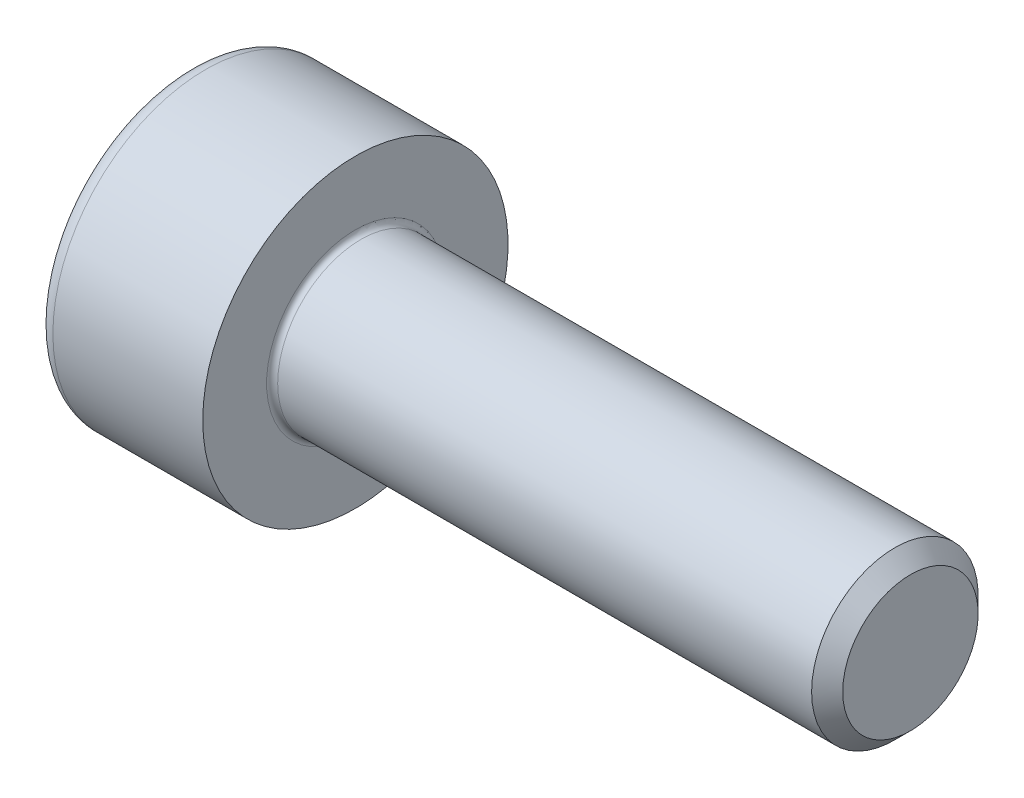
SolidWorks part; units mm, degrees
revolve "Base-Revolve" add sketch "BodySke"
sketch "BodySke" plane through (0, 0, 0) normal (0, 0, 1) x (1, 0, 0)
  line L0 (0, 0) -> (0, 2.75)
  line L1 (0, 2.75) -> (3, 2.75)
  line L2 (3, 2.75) -> (3, 1.5)
  line L3 (3, 1.5) -> (12.7195, 1.5)
  line L4 (13, 1.2195) -> (13, 0)
  line L5 (13, 0) -> (0, 0)
  line L6 (-31.75, 0) -> (127, 0) construction
  line L8 (13, 1.2195) -> (12.7195, 1.5)
  line L10 (13, -1.2195) -> (12.7195, -1.5) construction
  line L11 (3.5, 9.525) -> (3.5, 3.175) construction
  line L12 (3, 9.525) -> (3, 3.175) construction
  line L13 (-47, 9.525) -> (-47, 3.175) construction
  dimension "Head_ht" = 3
  dimension "Length" = 10
  dimension "Body_ch_ang" = 45
  dimension "Diameter" = 3
  dimension "Minor_dia" = 2.439
  dimension "Advance" = 0.5
  dimension "Thread_nom" = 10
  dimension "Thread_length" = 60
  dimension "Head_dia" = 5.5
cosmetic thread "ThreadCosmetic" [suppressed]
fillet "Fillet1" radius 0.1 1 edges at (3, 0, 1.5)
fillet "Fillet2" radius 0.3 1 edges at (0, 0, 2.75)
ref_plane "Plane1" through (0, 0, 0) normal (0, 0, 1) x (1, 0, 0)
ref_plane "Plane2" through (0, 0, 0) normal (0, 1, 0) x (1, 0, 0)
ref_plane "Plane3" through (0, 0, 0) normal (1, 0, 0) x (0, 0, -1)
sketch "Sketch2" plane through (0, 0, 0) normal (0, 0, 1) x (1, 0, 0)
  line L0 (0, 1.26) -> (1.3, 1.26)
  line L1 (1.3, 1.26) -> (2.0275, 0)
  line L2 (-31.75, 0) -> (127, 0) construction
  line L3 (2.0275, 0) -> (0, 0)
  line L4 (0, 0) -> (0, 1.26)
  line L6 (0, 0) -> (47.625, 0) construction
  dimension "D1" = 1.26
  dimension "D2" = 60
  dimension "Depth" = 1.3
revolve "Hex-PreBroach" cut sketch "Sketch2" angle 360 about L6
sketch "Sketch3" plane through (0, 0, 0) normal (-1, 0, 0) x (0, 0.5, 0.866)
  line L0 (0.7275, 1.26) -> (-0.7275, 1.26)
  line L1 (-0.7275, 1.26) -> (-1.4549, 0)
  line L2 (0.7275, 1.26) -> (1.4549, 0)
  line L3 (0.7275, -1.26) -> (1.4549, 0)
  line L4 (0.7275, -1.26) -> (-0.7275, -1.26)
  line L5 (-0.7275, -1.26) -> (-1.4549, 0)
  dimension "D1" = 1.26
  dimension "D2" = 1.26
  dimension "Hex_size" = 2.52
extrude "Hex" cut sketch "Sketch3" against normal blind 1.3
sketch "ThdSchSke" plane through (0, 0, 0) normal (0, 0, 1) x (1, 0, 0)
  line L0 (4.5, -1.2195) -> (4.3036, -1.5)
  line L1 (4.5, -1.2195) -> (4.6964, -1.5)
  line L2 (4.6964, -1.5) -> (4.6964, -1.875)
  line L3 (-3.175, 0) -> (5.1513, 0) construction
  line L4 (0, 2.45) -> (0, -2.45) construction
  line L5 (4.6964, -1.875) -> (4.3036, -1.875)
  line L6 (4.3036, -1.875) -> (4.3036, -1.5)
  dimension "Thread_minor" = 2.439
  dimension "Diameter" = 3
  dimension "Start" = 4.5
revolve "ThreadSchematic" [suppressed] cut sketch "ThdSchSke" angle 360 about L3
pattern_linear "ThdSchPat" [suppressed]
equation "\"D2@Sketch3\" = \"Hex_size@Sketch3\" / 2"
equation "\"D1@Sketch3\" = \"Hex_size@Sketch3\" / 2"
equation "\"D1@Sketch2\" = \"Hex_size@Sketch3\" / 2"
equation "\"Thread_minor@ThreadCosmetic\"  =  \"Minor_dia@BodySke\""
equation "\"Depth@Sketch2\" =  \"Key_eng@Hex\""
equation "\"Thread_length@ThreadCosmetic\" = ((sgn( (\"Length@BodySke\" - \"Advance@BodySke\" * 3.0) - \"Thread_nom@BodySke\" )-1)*( (\"Length@BodySke\" - \"Advance@BodySke\" * 3.0) - \"Thread_nom@BodySke\" ))/-2+ \"Thread_nom@BodySke\""
equation "\"Thread_minor@ThdSchSke\" = \"Minor_dia@BodySke\""
equation "\"Diameter@ThdSchSke\" = \"Diameter@BodySke\""
equation "\"Overcut@ThdSchSke\" = \"Diameter@BodySke\" * 1.25"
equation "\"Start@ThdSchSke\" = \"Head_ht@BodySke\" + \"Length@BodySke\" - \"Thread_length@ThreadCosmetic\"  '---Non-countersunk---"
equation "\"Num_threads@ThdSchPat\" = int( \"Thread_length@ThreadCosmetic\" / \"Advance@BodySke\" + 0.999 )  + 1"
equation "\"Advance@ThdSchPat\" = \"Thread_length@ThreadCosmetic\" /  (\"Num_threads@ThdSchPat\" - 1) 'relax it"
equation "\"Num_threads@ThdSchPat\" = \"Num_threads@ThdSchPat\" - sgn( \"Num_threads@ThdSchPat\" - 1) '---chamfered tips only---"
